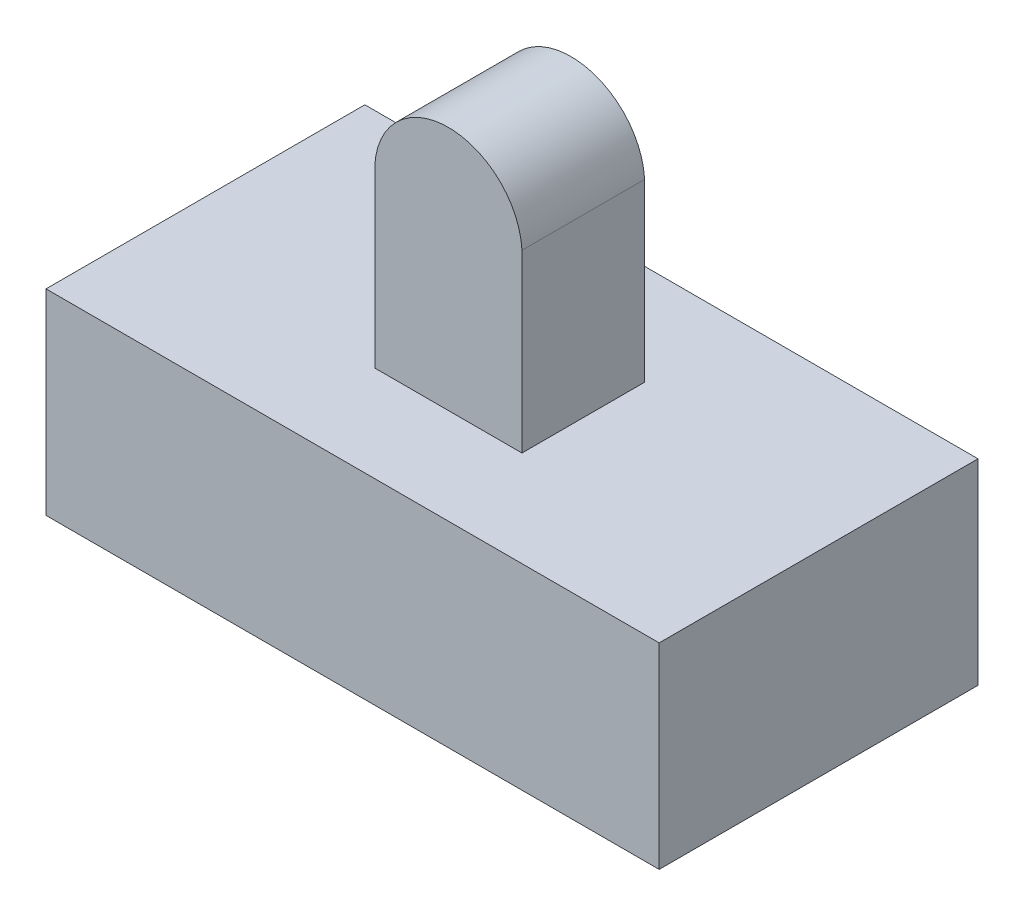
SolidWorks part; units mm, degrees
ref_plane "Front Plane" through (0, 0, 0) normal (0, 0, 1) x (1, 0, 0)
ref_plane "Top Plane" through (0, 0, 0) normal (0, 1, 0) x (1, 0, 0)
ref_plane "Right Plane" through (0, 0, 0) normal (1, 0, 0) x (0, 0, -1)
sketch "Sketch3" plane through (0, 0, 0) normal (0, 1, 0) x (1, 0, 0)
  line L1 (-5.8247, 4.6907) -> (19.1753, 4.6907)
  line L2 (-5.8247, 4.6907) -> (-5.8247, -8.3093)
  line L3 (-5.8247, -8.3093) -> (19.1753, -8.3093)
  line L4 (19.1753, 4.6907) -> (19.1753, -8.3093)
  dimension "D1" = 13
  dimension "D2" = 25
extrude "Boss-Extrude1" add sketch "Sketch3" along normal blind 8
sketch "Sketch4" plane through (0, 0, 0) normal (0, -1, 0) x (1, 0, 0)
  line L1 (9.3674, 3.3941) -> (3.3674, 3.3941)
  line L2 (9.3674, 3.3941) -> (9.3674, 0.2941)
  line L3 (9.3674, 0.2941) -> (3.3674, 0.2941)
  line L4 (3.3674, 3.3941) -> (3.3674, 0.2941)
  dimension "D1" = 3.1
  dimension "D2" = 6
extrude "Cut-Extrude1" cut sketch "Sketch4" against normal blind 5
sketch "Sketch5" plane through (0, 8, 0) normal (0, 1, 0) x (1, 0, 0)
  line L0 (9.6753, 0.5975) -> (3.6753, 0.5975)
  line L1 (9.6753, 0.5975) -> (9.6753, -4.4025)
  line L2 (9.6753, -4.4025) -> (3.6753, -4.4025)
  line L3 (3.6753, 0.5975) -> (3.6753, -4.4025)
  line L4 (19.1753, -8.3093) -> (19.1753, 4.6907) construction
  line L5 (-5.8247, 4.6907) -> (-5.8247, -8.3093) construction
  dimension "D1" = 9.5
  dimension "D2" = 9.5
  dimension "D3" = 5
extrude "Boss-Extrude2" add sketch "Sketch5" along normal blind 10
sketch "Sketch6" plane through (0, 0, -0.5975) normal (0, 0, -1) x (-1, 0, 0)
  line L0 (-9.6753, 18) -> (-9.6753, 8) construction
  line L1 (-3.6753, 18) -> (-3.6753, 8) construction
  line L2 (-9.6753, 14.8295) -> (-9.6753, 18)
  line L3 (-9.6753, 18) -> (-3.6753, 18)
  line L4 (-3.6753, 18) -> (-3.6753, 14.8295)
  arc A0 (-9.6753, 14.8295) -> (-3.6753, 14.8295) centre (-6.6753, 14.9954) cw
  line M3 (-3.6753, 18) -> (-9.6753, 18)
  line M4 (-9.6753, 18) -> (-9.6753, 8)
extrude "Cut-Extrude2" cut sketch "Sketch6" against normal blind 10 contours A0 L4 M3 | A0 L3 M4
